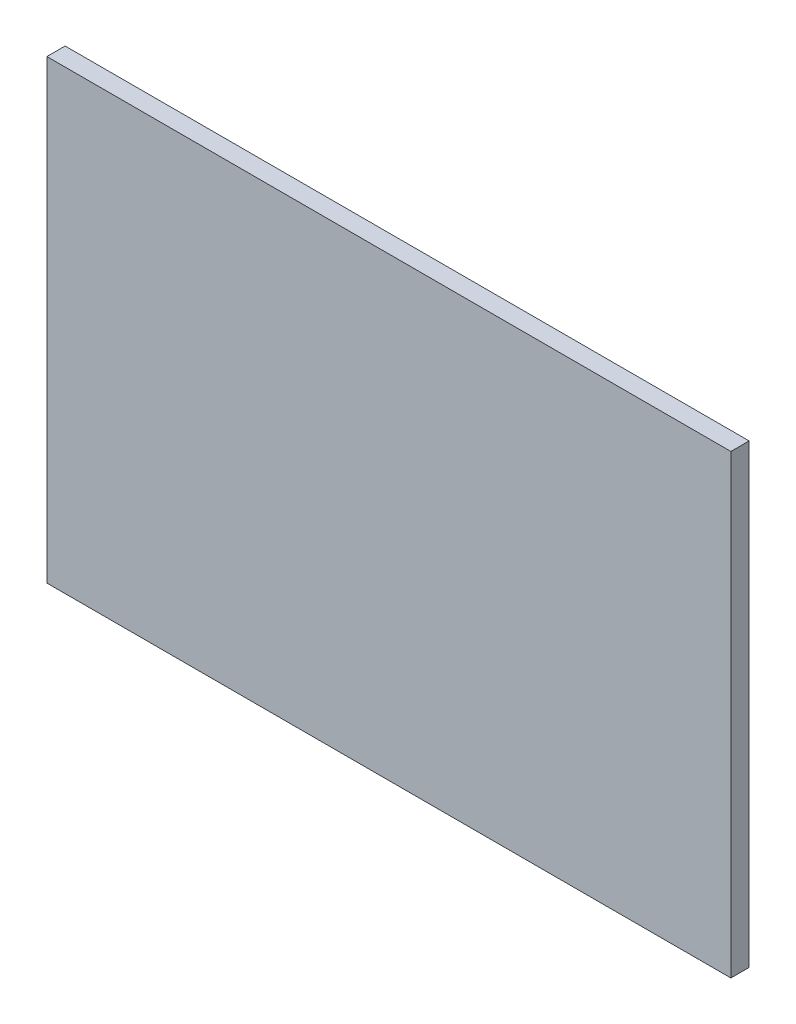
SolidWorks part; units mm, degrees
material "Glass"
ref_plane "Front Plane" through (0, 0, 0) normal (0, 0, 1) x (1, 0, 0)
ref_plane "Top Plane" through (0, 0, 0) normal (0, 1, 0) x (1, 0, 0)
ref_plane "Right Plane" through (0, 0, 0) normal (1, 0, 0) x (0, 0, -1)
sketch "Sketch1" plane through (0, 0, 0) normal (0, 1, 0) x (1, 0, 0)
  line L0 (0, -21) -> (0, 21) construction
  line L2 (-75, -21) -> (75, -21)
  line L3 (-75, -21) -> (-75, -25)
  line L4 (-75, -25) -> (75, -25)
  line L5 (75, -21) -> (75, -25)
  line L6 (-75, 21) -> (75, 21)
  line L7 (-75, 21) -> (-75, 25)
  line L8 (-75, 25) -> (75, 25)
  line L9 (75, 21) -> (75, 25)
  point P4 (0, 0)
  dimension "D1" = 42
  dimension "D2" = 150
  dimension "D3" = 4
extrude "Boss-Extrude1" add sketch "Sketch1" along normal blind 100 contours L5 L2 L3 L4
equation "\"glass_width\" = 150"
equation "\"glass_height\"= 100"
equation "\"glass_thickness\"= 4"
equation "\"brood_space\"= 42"
